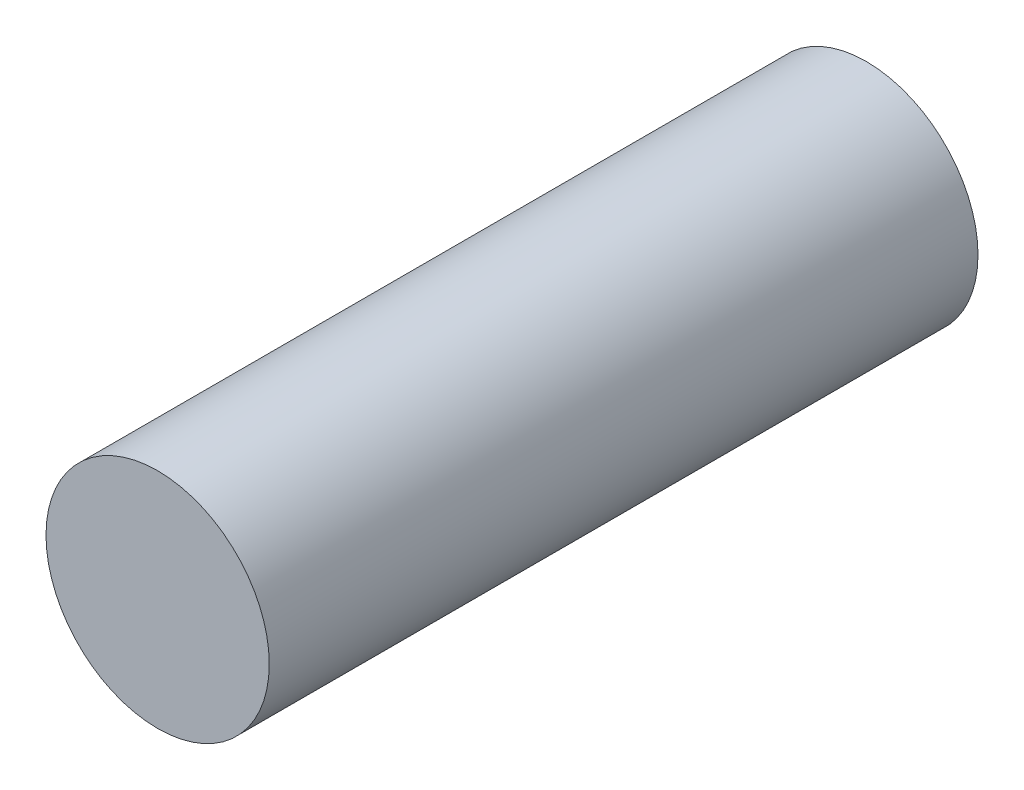
SolidWorks part; units mm, degrees
ref_plane "Front Plane" through (0, 0, 0) normal (0, 0, 1) x (1, 0, 0)
ref_plane "Top Plane" through (0, 0, 0) normal (0, 1, 0) x (1, 0, 0)
ref_plane "Right Plane" through (0, 0, 0) normal (1, 0, 0) x (0, 0, -1)
sketch "Sketch1" plane through (0, 0, 0) normal (0, 0, 1) x (1, 0, 0)
  circle A0 centre (0, 0) radius 16.002
  dimension "D1" = 32.004
extrude "Boss-Extrude1" add sketch "Sketch1" along normal blind 101.6
